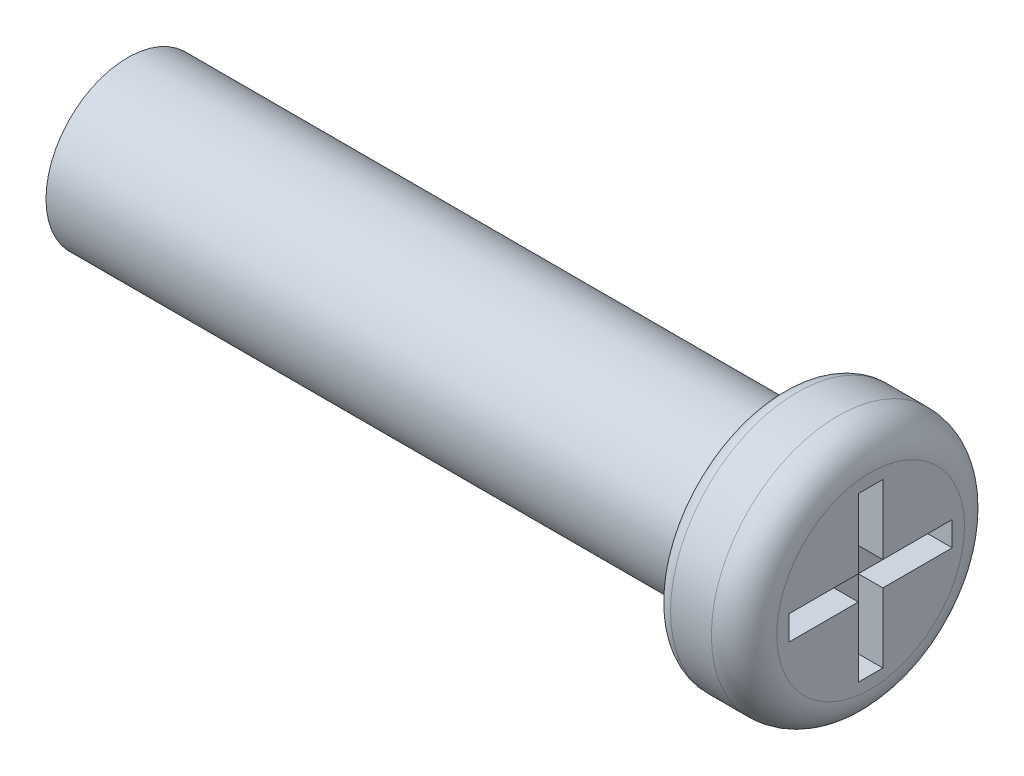
SolidWorks part; units mm, degrees
ref_plane "Plano frontal" through (0, 0, 0) normal (0, 0, 1) x (1, 0, 0)
ref_plane "Plano superior" through (0, 0, 0) normal (0, 1, 0) x (1, 0, 0)
ref_plane "Plano direito" through (0, 0, 0) normal (1, 0, 0) x (0, 0, -1)
sketch "Esboço1" plane through (0, 0, 0) normal (1, 0, 0) x (0, 0, -1)
  circle A0 centre (0, 0) radius 1
  dimension "D1" = 2
extrude "Ressalto-extrusão1" add sketch "Esboço1" along normal blind 25
sketch "Esboço2" plane through (25, 0, 0) normal (1, 0, 0) x (0, 0, -1)
  circle A1 centre (0, 0) radius 1.55
extrude "Ressalto-extrusão2" add sketch "Esboço2" along normal blind 1.1
thread "Rosca1" pitch 0.4 start angle 0, offset 1, length 50, pitch 0.4, diameter 2
ref_plane "Plano1" through (-1, 0, -1) normal (0, -1, 0) x (0, 0, -1)
sketch "Perfil da rosca1" plane through (-1, 0, -1) normal (0, -1, 0) x (0, 0, -1)
  line L0 (0, 0) -> (0, 0.4) construction
  line L1 (0, 0) -> (0.2165, 0.125)
  line L2 (0.2165, 0.125) -> (0.2165, 0.175)
  line L3 (0.2165, 0.175) -> (0, 0.3)
  line L4 (0.2165, 0.15) -> (0, 0.15) construction
  line L11 (0, 0) -> (0, 0.3)
  point P2 (0, 0)
  dimension "Pitch" = 0.4
  dimension "Profile_Angle" = 60
  dimension "Profile_Land" = 0.05
  dimension "Profile_Height" = 0.2165
sketch "Sketch1" plane through (0, 0, 0) normal (-1, 0, 0) x (0, 0, 1)
  circle A0 centre (0, 0) radius 1
extrude "Cut-Extrude1" cut sketch "Sketch1" against normal blind 17
sketch "Sketch2" plane through (26.1, 0, 0) normal (1, 0, 0) x (0, 0, -1)
  line L1 (0.15, 1) -> (-0.15, 1)
  line L2 (0.15, 1) -> (0.15, -1)
  line L3 (0.15, -1) -> (-0.15, -1)
  line L4 (-0.15, 1) -> (-0.15, -1)
  line L5 (0.15, 1) -> (-0.15, -1) construction
  line L6 (0.15, -1) -> (-0.15, 1) construction
  line L7 (1, 0.15) -> (-1, 0.15)
  line L8 (1, 0.15) -> (1, -0.15)
  line L9 (1, -0.15) -> (-1, -0.15)
  line L10 (-1, 0.15) -> (-1, -0.15)
  line L11 (1, 0.15) -> (-1, -0.15) construction
  line L12 (1, -0.15) -> (-1, 0.15) construction
  point P0 (0, 0)
  point P6 (0, 0)
  dimension "D1" = 0.3
  dimension "D2" = 0.3
  dimension "D3" = 2
  dimension "D4" = 2
extrude "Cut-Extrude3" cut sketch "Sketch2" against normal blind 0.3 contours L9 L8 L7 L2 | L7 L10 L9 L4 | L7 L2 L1 L4 | L2 L9 L4 L3 | L9 L2 L7 L4
fillet "Fillet1" radius 0.4 1 edges at (26.1, 0, -1.55)
fillet "Fillet2" radius 0.2 1 edges at (25, 0, -1.55)
